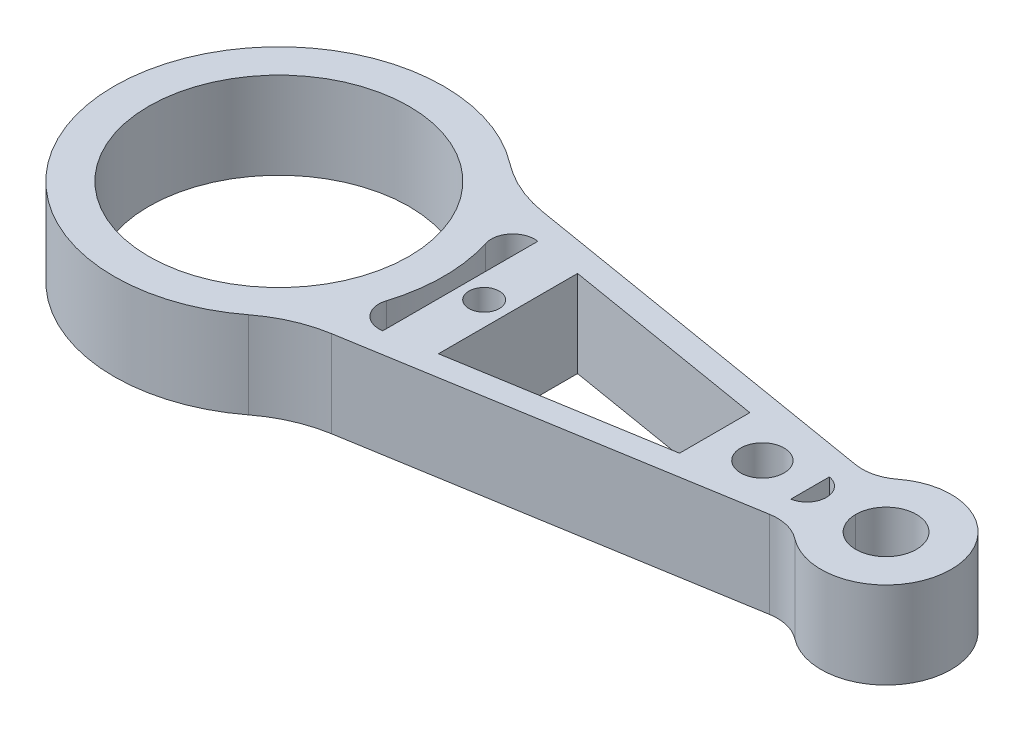
SolidWorks part; units mm, degrees
material "Plain Carbon Steel"
ref_plane "Front Plane" through (0, 0, 0) normal (0, 0, 1) x (1, 0, 0)
ref_plane "Top Plane" through (0, 0, 0) normal (0, 1, 0) x (1, 0, 0)
ref_plane "Right Plane" through (0, 0, 0) normal (1, 0, 0) x (0, 0, -1)
sketch "Sketch1" plane through (0, 0, 0) normal (0, 1, 0) x (1, 0, 0)
  line L0 (-70.1354, 0) -> (160.5153, 0) construction
  line L1 (154.2362, 4.7254) -> (162.3118, 3.3804)
  line L2 (161.8433, -3.4585) -> (154.2362, -4.7254)
  line L3 (27.9355, 25.7606) -> (128.0638, 9.0844)
  line L4 (128.0638, -9.0844) -> (27.9355, -25.7606)
  circle A0 centre (0, 0) radius 30
  circle A1 centre (140, 0) radius 7
  arc A2 (27.9355, 25.7606) -> (27.9355, -25.7606) centre (0, 0) ccw
  arc A3 (128.0638, -9.0844) -> (128.0638, 9.0844) centre (140, 0) ccw
  dimension "D2" = 60
  dimension "D3" = 76
  dimension "D4" = 14
  dimension "D5" = 30
  dimension "D1" = 140
extrude "Boss-Extrude1" add sketch "Sketch1" along normal mid plane 20 contours L0 A2 L4 A3 A1 A0 | A2 L0 A0 A1 A3 L3
fillet "Fillet1" radius 30 2 edges at (27.9355, 0, 25.7606) (27.9355, 0, -25.7606)
fillet "Fillet2" radius 10 2 edges at (128.0638, 0, 9.0844) (128.0638, 0, -9.0844)
sketch "Sketch2" plane through (0, 10, 0) normal (0, 1, 0) x (1, 0, 0)
  line L0 (0, 0) -> (172.9584, 0) construction
  line L1 (41.8286, 17.871) -> (122.4784, 4.4389)
  line L2 (122.4784, -4.4389) -> (41.8286, -17.871)
  line L3 (36.4938, 24.3352) -> (123.0688, 9.9163) construction
  arc A0 (36.2389, 11.4344) -> (36.2389, -11.4344) centre (0, 0) cw
  arc A1 (36.2389, 11.4344) -> (41.8286, 17.871) centre (41.0071, 12.9389) cw
  arc A2 (36.2389, -11.4344) -> (41.8286, -17.871) centre (41.0071, -12.9389) ccw
  arc A3 (122.4784, -4.4389) -> (122.4784, 4.4389) centre (121.7391, 0) ccw
  circle A4 centre (0, 0) radius 30 construction
  dimension "D1" = 5
  dimension "D2" = 4.5
  dimension "D4" = 8
  dimension "D3" = 5.5
extrude "Cut-Extrude1" cut sketch "Sketch2" against normal through all
split line "Split Line1"
sketch "Sketch3" plane through (0, 10, 0) normal (0, 1, 0) x (1, 0, 0)
  line L1 (122.4784, 4.4389) -> (41.8286, 17.871) construction
  line L4 (41.8286, -17.871) -> (122.4784, -4.4389) construction
  line L6 (100.4784, 8.1029) -> (122.4784, 4.4389)
  line L7 (122.4784, 4.4389) -> (122.4784, -4.4389)
  line L8 (122.4784, -4.4389) -> (100.4784, -8.1029)
  line L9 (100.4784, -8.1029) -> (100.4784, 8.1029)
  line L10 (41.8286, 17.871) -> (52.8286, 16.0389)
  line L11 (52.8286, 16.0389) -> (52.8286, -16.0389)
  line L12 (52.8286, -16.0389) -> (41.8286, -17.871)
  line L13 (41.8286, -17.871) -> (41.8286, 17.871)
  dimension "D1" = 11
  dimension "D2" = 22
extrude "Boss-Extrude2" add sketch "Sketch3" against normal blind 20
sketch "Sketch4" plane through (0, 10, 0) normal (0, 1, 0) x (1, 0, 0)
  line L0 (0, 0) -> (187.7433, 0) construction
  line L3 (52.8286, -16.0389) -> (52.8286, 16.0389) construction
  line L4 (122.4784, -4.4389) -> (122.4784, 4.4389) construction
  circle A0 centre (47.3286, 0) radius 3.5
  circle A1 centre (111.4784, 0) radius 5
  point P7 (47.8067, 0)
  point P8 (0, 0)
  dimension "D1" = 10
  dimension "D2" = 7
  dimension "D3" = 5.5
  dimension "D4" = 11
extrude "Cut-Extrude2" cut sketch "Sketch4" against normal through all
